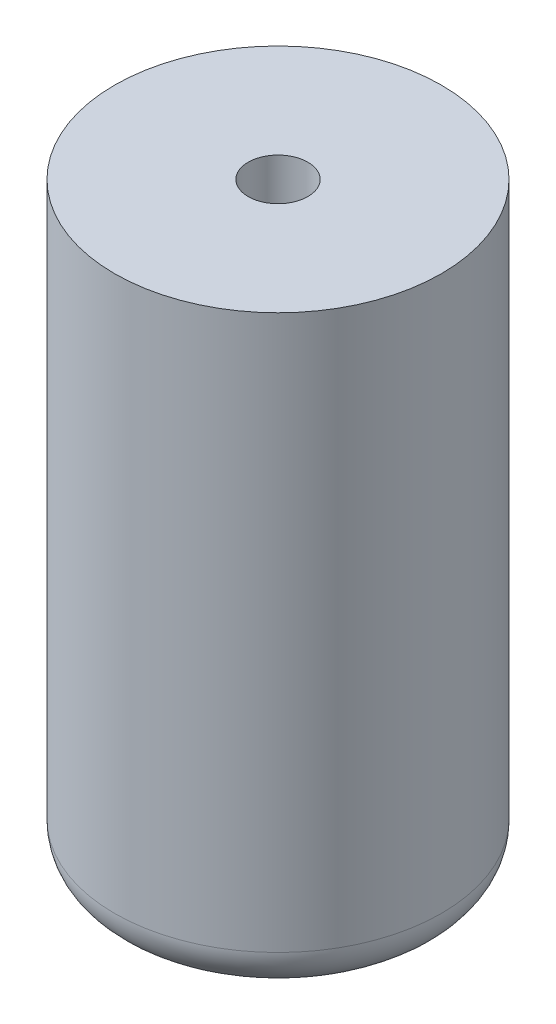
SolidWorks part; units mm, degrees
ref_plane "Front" through (0, 0, 0) normal (0, 0, 1) x (1, 0, 0)
ref_plane "Top" through (0, 0, 0) normal (0, 1, 0) x (1, 0, 0)
ref_plane "Right" through (0, 0, 0) normal (1, 0, 0) x (0, 0, -1)
sketch "Sketch1" plane through (0, 0, 0) normal (0, 1, 0) x (1, 0, 0)
  circle A0 centre (0, 0) radius 11.5
  dimension "D1" = 23
extrude "Boss-Extrude1" add sketch "Sketch1" along normal blind 42
fillet "Fillet1" radius 3 1 edges at (0, 0, 11.5)
sketch "Sketch3" plane through (0, 42, 0) normal (0, 1, 0) x (1, 0, 0)
  circle A0 centre (0, 0) radius 2.1
  dimension "D1" = 4.2
extrude "Cut-Extrude1" cut sketch "Sketch3" against normal blind 10
